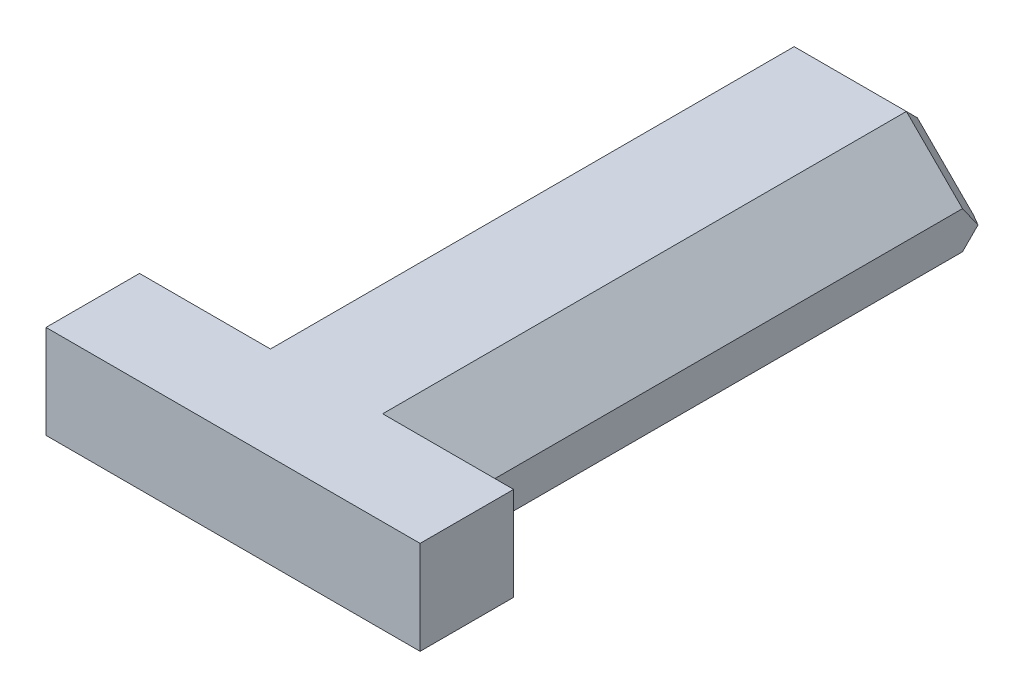
SolidWorks part; units mm, degrees
ref_plane "前视基准面" through (0, 0, 0) normal (0, 0, 1) x (1, 0, 0)
ref_plane "上视基准面" through (0, 0, 0) normal (0, 1, 0) x (1, 0, 0)
ref_plane "右视基准面" through (0, 0, 0) normal (1, 0, 0) x (0, 0, -1)
sketch "草图1" plane through (0, 0, 0) normal (0, 0, 1) x (1, 0, 0)
  line L0 (-19.832, -9.8757) -> (-3.832, -9.8757)
  line L1 (-11.832, -9.8757) -> (-11.832, -4.8757) construction
  line L2 (-3.832, -9.8757) -> (-8.832, -4.8757)
  line L3 (-8.832, -4.8757) -> (-14.832, -4.8757)
  line L4 (-14.832, -4.8757) -> (-19.832, -9.8757)
extrude "凸台-拉伸1" add sketch "草图1" along normal blind 29
sketch "草图3" plane through (0, -9.8757, 0) normal (0, -1, 0) x (1, 0, 0)
  line L0 (-11.832, 29) -> (-1.832, 29)
  line L1 (-19.832, 29) -> (-3.832, 29) construction
  line L2 (-1.832, 29) -> (-1.832, 34)
  line L3 (-1.832, 34) -> (-21.832, 34)
  line L4 (-21.832, 34) -> (-21.832, 29)
  line L5 (-21.832, 29) -> (-11.832, 29)
extrude "凸台-拉伸2" add sketch "草图3" against normal up to surface (5 mm away) up to face at (-11.832, -4.8757, 14.5)
chamfer "倒角1" distance 1 angle 45 4 edges at (-11.832, -9.8757, 0) (-6.332, -7.3757, 0) (-11.832, -4.8757, 0) (-17.332, -7.3757, 0)
sketch "草图4" plane through (0, 0, 29) normal (0, 0, -1) x (-1, 0, 0)
  line L1 (3.832, -9.8757) -> (5.832, -9.8757)
  line L2 (3.832, -9.8757) -> (3.832, -6.7717)
  line L3 (3.832, -6.7717) -> (5.832, -6.7717)
  line L4 (5.832, -9.8757) -> (5.832, -6.7717)
  line L5 (19.832, -9.8757) -> (17.832, -9.8757)
  line L6 (19.832, -9.8757) -> (19.832, -6.5496)
  line L7 (19.832, -6.5496) -> (17.832, -6.5496)
  line L8 (17.832, -9.8757) -> (17.832, -6.5496)
  dimension "D1" = 2
  dimension "D2" = 2
extrude "切除-拉伸1" cut sketch "草图4" along normal through all
